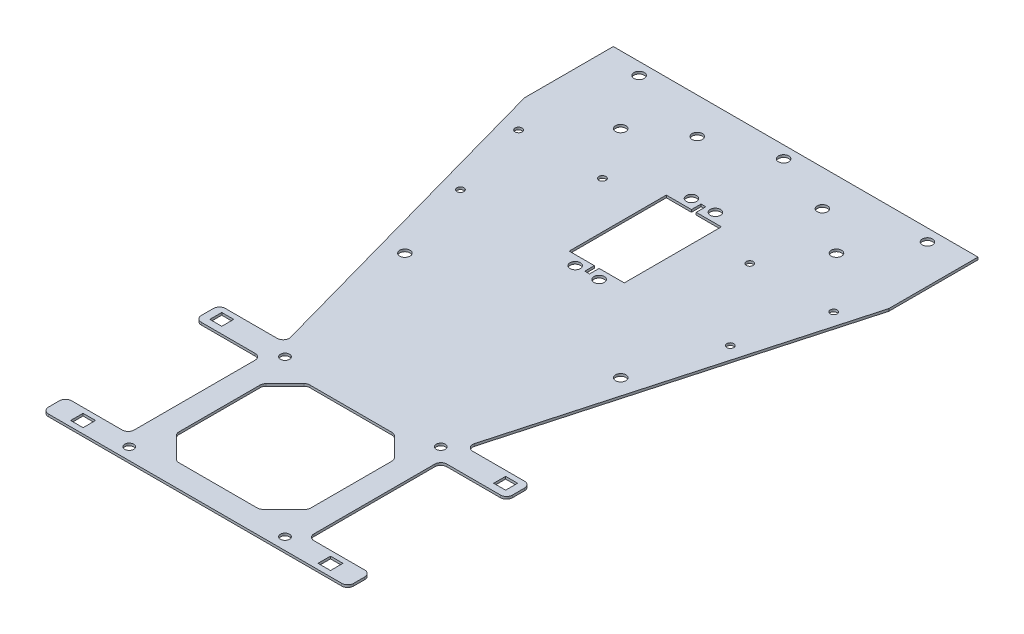
SolidWorks part; units mm, degrees
ref_plane "Front Plane" through (0, 0, 0) normal (0, 0, 1) x (1, 0, 0)
ref_plane "Top Plane" through (0, 0, 0) normal (0, 1, 0) x (1, 0, 0)
ref_plane "Right Plane" through (0, 0, 0) normal (1, 0, 0) x (0, 0, -1)
sketch "Sketch26" plane through (0, 0, 0) normal (0, 1, 0) x (1, 0, 0)
  line L0 (76.0133, 88.8235) -> (76.0133, 51.6238)
  line L1 (76.0133, 88.8235) -> (-76.1021, 88.8235)
  line L2 (38.3828, -83.5273) -> (75.5055, 49.8)
  line L3 (45.09, 63.6995) -> (45.09, 54.4377) construction
  line L4 (76.0133, 51.6238) -> (63.6741, 55.0595) construction
  line L5 (30, -161.7164) -> (61.1569, -161.7164)
  line L6 (76.0133, 51.6238) -> (75.5055, 49.8)
  line L7 (27.5, -140.9451) -> (27.5, -107.1019)
  line L8 (11.5777, 5.7174) -> (11.5777, 46.2174)
  line L9 (1.09, 1.7174) -> (-0.91, 1.7174)
  line L10 (-11.3978, 5.7174) -> (-11.3978, 46.2174)
  line L11 (1.09, 5.7174) -> (11.5777, 5.7174)
  line L12 (0, 119.0602) -> (0, 33.226) construction
  line L13 (-18.8823, -97.4487) -> (-26.7576, -105.324)
  line L14 (18.8823, -97.4487) -> (26.7678, -105.3342)
  line L15 (-44.91, -22.0666) -> (-44.91, -53.7446) construction
  line L16 (-29.9883, -161.7164) -> (30, -161.7164)
  line L17 (-16.3184, -152.1151) -> (16.3184, -152.1151)
  line L18 (1.09, 50.2174) -> (-0.91, 50.2174)
  line L19 (-18.0861, -151.3829) -> (-26.7642, -142.7048)
  line L20 (18.0849, -151.3841) -> (26.7666, -142.7141)
  line L21 (45.09, -22.0755) -> (45.09, -53.7446) construction
  line L22 (-27.4964, -140.9365) -> (-27.4898, -107.0913)
  line L23 (-34.9883, -161.7164) -> (-61.1569, -161.7164)
  line L24 (-44.91, 63.6995) -> (-44.91, 54.4377) construction
  line L25 (-63.6569, -159.2164) -> (-63.6569, -154.6151)
  line L26 (-61.1569, -152.1151) -> (-40, -152.1151)
  line L27 (-49, -154.2438) -> (-49, -159.4438)
  line L28 (-76.1021, 51.7763) -> (-76.1021, 88.8235)
  line L29 (1.09, 46.2174) -> (11.5777, 46.2174)
  line L30 (-54.2, -156.2865) -> (-54.2, -159.4438)
  line L31 (-37.5, -149.6151) -> (-37.5, -99.2164)
  line L32 (-49, -154.2438) -> (-54.2, -154.2438)
  line L33 (-0.91, 1.7174) -> (-0.91, 5.7174)
  line L34 (-0.91, 50.2174) -> (-0.91, 46.2174)
  line L35 (-54.2, -154.2438) -> (-54.2, -159.4438)
  line L36 (1.09, 50.2174) -> (1.09, 46.2174)
  line L37 (-0.91, 46.2174) -> (-11.3978, 46.2174)
  line L38 (1.09, 1.7174) -> (1.09, 5.7174)
  line L39 (-49, -159.4438) -> (-54.2, -159.4438)
  line L40 (49, -159.4438) -> (54.2, -159.4438)
  line L41 (54.2, -154.2438) -> (54.2, -159.4438)
  line L42 (49, -154.2438) -> (54.2, -154.2438)
  line L43 (54.2, -156.2865) -> (54.2, -159.4438)
  line L44 (49, -154.2438) -> (49, -159.4438)
  line L45 (61.1569, -152.1151) -> (40, -152.1151)
  line L46 (63.6569, -159.2164) -> (63.6569, -154.6151)
  line L47 (40.7912, -86.6979) -> (62.3785, -86.6979)
  line L48 (64.8785, -89.1979) -> (64.8785, -94.2164)
  line L49 (62.3785, -96.7164) -> (40, -96.7164)
  line L50 (-0.91, 5.7174) -> (-11.3978, 5.7174)
  line L51 (56.7, -88.896) -> (56.7, -93.896)
  line L52 (61.7, -88.896) -> (61.7, -93.896)
  line L53 (-29.9883, -161.7164) -> (-34.9883, -161.7164)
  line L54 (-38.3828, -83.5273) -> (-76.1021, 51.7763)
  line L55 (-17.1145, -96.7164) -> (17.1145, -96.7164)
  line L56 (56.7, -88.896) -> (61.7, -88.896)
  line L57 (56.7, -93.896) -> (61.7, -93.896)
  line L58 (-56.7, -93.896) -> (-61.7, -93.896)
  line L59 (-56.7, -88.896) -> (-61.7, -88.896)
  line L60 (-61.7, -88.896) -> (-61.7, -93.896)
  line L61 (-56.7, -88.896) -> (-56.7, -93.896)
  line L62 (-62.3785, -96.7164) -> (-40, -96.7164)
  line L63 (-64.8785, -89.1979) -> (-64.8785, -94.2164)
  line L64 (-40.7912, -86.6979) -> (-62.3785, -86.6979)
  line L69 (37.5, -149.6151) -> (37.5, -99.2164)
  circle A0 centre (45.09, 60.7174) radius 2.15
  circle A1 centre (45.09, -29.2826) radius 2.15
  circle A2 centre (5.09, 50.2174) radius 2.15
  circle A3 centre (5.09, 1.7174) radius 2.15
  circle A4 centre (-26.1021, 73.8235) radius 2.15
  circle A5 centre (0, 83.748) radius 2.15
  circle A6 centre (26.1021, 73.8235) radius 2.15
  arc A7 (18.0849, -151.3841) -> (16.3184, -152.1151) centre (16.3184, -149.6151) cw
  arc A8 (27.5, -140.9451) -> (26.7666, -142.7141) centre (25, -140.9451) cw
  arc A9 (27.5, -107.1019) -> (26.7678, -105.3342) centre (25, -107.1019) ccw
  circle A10 centre (60, 83.7476) radius 2.15
  circle A11 centre (-32.5, -91.7164) radius 1.875
  circle A12 centre (-32.5, -156.7164) radius 1.875
  arc A13 (18.8823, -97.4487) -> (17.1145, -96.7164) centre (17.1145, -99.2164) ccw
  circle A14 centre (-56.2751, 5.2271) radius 1.45
  circle A15 centre (5.09, 50.2174) radius 2.15
  circle A16 centre (-65.7103, 38.9314) radius 1.45
  circle A17 centre (-4.91, 50.2174) radius 2.15
  circle A18 centre (-60.2633, 83.7476) radius 2.15
  arc A19 (-27.4898, -107.0913) -> (-26.7576, -105.324) centre (-24.9898, -107.0918) cw
  arc A20 (-17.1145, -96.7164) -> (-18.8823, -97.4487) centre (-17.1145, -99.2164) ccw
  arc A21 (-16.3184, -152.1151) -> (-18.0861, -151.3829) centre (-16.3184, -149.6151) cw
  arc A22 (-26.7642, -142.7048) -> (-27.4964, -140.9365) centre (-24.9964, -140.937) cw
  arc A23 (37.5, -99.2164) -> (40, -96.7164) centre (40, -99.2164) cw
  arc A24 (-37.5, -149.6151) -> (-40, -152.1151) centre (-40, -149.6151) cw
  circle A25 centre (-4.91, 1.7174) radius 2.15
  circle A26 centre (-4.91, 50.2174) radius 2.15
  circle A27 centre (-44.91, -29.2826) radius 2.15
  circle A28 centre (-44.91, 60.7174) radius 2.15
  arc A29 (64.8785, -94.2164) -> (62.3785, -96.7164) centre (62.3785, -94.2164) cw
  arc A30 (-61.1569, -161.7164) -> (-63.6569, -159.2164) centre (-61.1569, -159.2164) cw
  arc A31 (-63.6569, -154.6151) -> (-61.1569, -152.1151) centre (-61.1569, -154.6151) cw
  arc A32 (63.6569, -154.6151) -> (61.1569, -152.1151) centre (61.1569, -154.6151) ccw
  arc A33 (61.1569, -161.7164) -> (63.6569, -159.2164) centre (61.1569, -159.2164) ccw
  arc A34 (37.5, -149.6151) -> (40, -152.1151) centre (40, -149.6151) ccw
  circle A35 centre (30.728, 38.917) radius 1.45
  arc A36 (64.8785, -89.1979) -> (62.3785, -86.6979) centre (62.3785, -89.1979) ccw
  arc A37 (40.7912, -86.6979) -> (38.3828, -83.5273) centre (40.7912, -84.1979) cw
  arc A38 (-40.7912, -86.6979) -> (-38.3828, -83.5273) centre (-40.7912, -84.1979) ccw
  arc A39 (-64.8785, -89.1979) -> (-62.3785, -86.6979) centre (-62.3785, -89.1979) cw
  arc A40 (-64.8785, -94.2164) -> (-62.3785, -96.7164) centre (-62.3785, -94.2164) ccw
  arc A41 (-37.5, -99.2164) -> (-40, -96.7164) centre (-40, -99.2164) ccw
  circle A42 centre (-30.728, 38.917) radius 1.45
  circle A50 centre (65.728, 38.917) radius 1.45
  circle A51 centre (56.34, 5.1996) radius 1.45
  circle A57 centre (32.5, -156.7164) radius 1.875
  circle A60 centre (32.5, -91.7164) radius 1.875
  point P38 (0, 88.8235)
  point P42 (0.09, 1.7174)
  point P48 (0, 78.8235)
  point P77 (18.15, -96.7164)
  point P83 (-18.15, -96.7164)
  point P96 (-17.3539, -152.1151)
  point P99 (-0.285, 50.2174)
  point P100 (0, -96.7164)
  point P107 (0.09, 1.7174)
  point P111 (0, 78.8235)
  point P119 (-0.0444, 88.8235)
  point P122 (0.09, 50.2174)
  point P126 (-0.0444, 88.8235)
  point P127 (0, 78.8235)
  point P128 (0.4649, 50.2174)
  point P137 (27.5, -96.7164)
  dimension "D6" = 4.3
  dimension "D13" = 15
  dimension "D14" = 11.5
  dimension "D15" = 5.2
  dimension "D16" = 5.2
  dimension "D10" = 4.3
  dimension "D21" = 35
  dimension "D7" = 50
  dimension "D8" = 4.3
  dimension "D22" = 10.5
  dimension "D4" = 48.5
  dimension "D11" = 4.3
  dimension "D36" = 65
  dimension "D37" = 5
  dimension "D38" = 2.9
  dimension "D41" = 2.9
  dimension "D47" = 3.75
  dimension "D54" = 60
  dimension "D33" = 4.3
  dimension "D51" = 4.3
  dimension "D53" = 4.3
  dimension "D9" = 2.5
  dimension "D23" = 2.9
  dimension "D17" = 2.5
  dimension "D12" = 5.0759
  dimension "D18" = 19.2
  dimension "D19" = 5
  dimension "D20" = 5
  dimension "D25" = 4
  dimension "D29" = 5
  dimension "D30" = 31
  dimension "D32" = 4
  dimension "D34" = 15
  dimension "D35" = 5
  dimension "D42" = 35
  dimension "D44" = 40
  dimension "D48" = 5
  dimension "D49" = 6.5
  dimension "D50" = 6.5
extrude "Boss-Extrude6" add sketch "Sketch26" along normal blind 1
